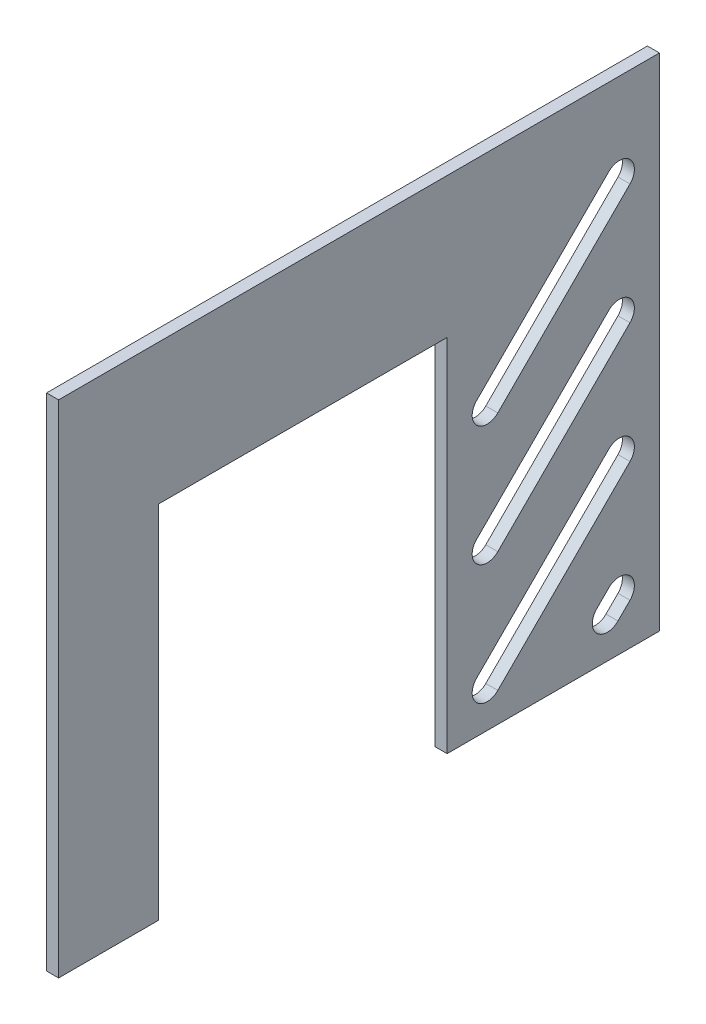
SolidWorks part; units mm, degrees
ref_plane "Front Plane" through (0, 0, 0) normal (0, 0, 1) x (1, 0, 0)
ref_plane "Top Plane" through (0, 0, 0) normal (0, 1, 0) x (1, 0, 0)
ref_plane "Right Plane" through (0, 0, 0) normal (1, 0, 0) x (0, 0, -1)
sketch "Sketch1" plane through (0, 0, 0) normal (1, 0, 0) x (0, 0, -1)
  line L0 (0, 0) -> (50, 0)
  line L2 (0, 0) -> (0, 250)
  line L3 (0, 250) -> (300, 250)
  line L4 (300, 0) -> (300, 250)
  line L5 (50, 0) -> (50, 180)
  line L6 (50, 180) -> (194, 180)
  line L7 (194, 180) -> (194, 0)
  line L8 (300, 0) -> (194, 0)
  line L9 (50, 0) -> (0, 0)
  line L10 (280, 20) -> (214, 86) construction
  line L11 (300, 0) -> (280, 0)
  line L12 (300, 0) -> (300, 20)
  line L13 (300, 20) -> (280, 20) construction
  line L14 (280, 0) -> (280, 20) construction
  line L15 (280, 20) -> (214, 20) construction
  line L16 (280, 20) -> (280, 86) construction
  line L17 (280, 86) -> (214, 86) construction
  line L18 (214, 20) -> (214, 86) construction
  line L19 (214, 86) -> (194, 86) construction
  line L20 (214, 86) -> (214, 106) construction
  line L21 (214, 106) -> (194, 106) construction
  line L22 (194, 86) -> (194, 106)
  line L23 (274.6967, 14.6967) -> (208.6967, 80.6967)
  line L24 (285.3033, 25.3033) -> (219.3033, 91.3033)
  arc A0 (274.6967, 14.6967) -> (285.3033, 25.3033) centre (280, 20) ccw
  arc A1 (219.3033, 91.3033) -> (208.6967, 80.6967) centre (214, 86) ccw
  point P18 (247, 53)
  dimension "D1" = 250
  dimension "D2" = 300
  dimension "D3" = 180
  dimension "D4" = 144
  dimension "D5" = 250
  dimension "D6" = 20
  dimension "D7" = 20
  dimension "D8" = 66
  dimension "D9" = 66
  dimension "D10" = 20
  dimension "D11" = 15
extrude "Boss-Extrude1" add sketch "Sketch1" along normal blind 6 contours L8 L4 L3 L2 L0 L5 L6 L7
sketch "Sketch2" plane through (0, 0, 0) normal (-1, 0, 0) x (0, 0, 1)
  line L0 (-194, 180) -> (-194, 0) construction
  line L1 (-300, 0) -> (-194, 0)
  line L2 (-300, 0) -> (-300, 107.9511)
  line L3 (-300, 107.9511) -> (-194, 107.9511)
  line L4 (-194, 0) -> (-194, 107.9511)
extrude "Boss-Extrude3" add sketch "Sketch2" against normal up to surface (6 mm away) up to face at (6, 53, -247)
sketch "Sketch3" plane through (0, 0, 0) normal (-1, 0, 0) x (0, 0, 1)
  line L0 (-194, 0) -> (-194, 288) construction
  line L1 (-300, 180) -> (-300, 0) construction
  line L2 (-194, 0) -> (-300, 0) construction
  line L3 (-214, 20) -> (-280, 86) construction
  line L4 (-194, 0) -> (-214, 0) construction
  line L5 (-194, 0) -> (-194, 20) construction
  line L6 (-194, 20) -> (-214, 20) construction
  line L7 (-214, 0) -> (-214, 20) construction
  line L8 (-214, 20) -> (-280, 20) construction
  line L9 (-214, 20) -> (-214, 86) construction
  line L10 (-214, 86) -> (-280, 86) construction
  line L11 (-280, 20) -> (-280, 86) construction
  line L12 (-280, 86) -> (-300, 86) construction
  line L13 (-280, 86) -> (-280, 106) construction
  line L14 (-280, 106) -> (-300, 106) construction
  line L15 (-300, 86) -> (-300, 106) construction
  line L16 (-219.3033, 14.6967) -> (-285.3033, 80.6967)
  line L17 (-208.6967, 25.3033) -> (-274.6967, 91.3033)
  line L18 (-280, 86) -> (-280, 26) construction
  line L19 (-214, 20) -> (-274, 20) construction
  line L20 (-274, 20) -> (-280, 26) construction
  line L21 (-279.3033, 14.6967) -> (-285.3033, 20.6967)
  line L22 (-268.6967, 25.3033) -> (-274.6967, 31.3033)
  line L23 (-194, 108) -> (-194, 288) construction
  line L24 (-300, 288) -> (-194, 288) construction
  line L25 (-280, 268) -> (-214, 268) construction
  line L26 (-214, 268) -> (-214, 202) construction
  line L27 (-214, 202) -> (-214, 262) construction
  line L28 (-280, 268) -> (-220, 268) construction
  line L29 (-220, 268) -> (-214, 262) construction
  line L30 (-214.6967, 273.3033) -> (-208.6967, 267.3033)
  line L31 (-225.3033, 262.6967) -> (-219.3033, 256.6967)
  arc A0 (-219.3033, 14.6967) -> (-208.6967, 25.3033) centre (-214, 20) ccw
  arc A1 (-274.6967, 91.3033) -> (-285.3033, 80.6967) centre (-280, 86) ccw
  arc A2 (-279.3033, 14.6967) -> (-268.6967, 25.3033) centre (-274, 20) ccw
  arc A3 (-274.6967, 31.3033) -> (-285.3033, 20.6967) centre (-280, 26) ccw
  arc A4 (-214.6967, 273.3033) -> (-225.3033, 262.6967) centre (-220, 268) ccw
  arc A5 (-219.3033, 256.6967) -> (-208.6967, 267.3033) centre (-214, 262) ccw
  point P13 (-247, 53)
  point P22 (-277, 23)
  point P37 (-217, 265)
  dimension "D10" = 7.5
  dimension "D15" = 7.5
  dimension "D1" = 288
  dimension "D2" = 20
  dimension "D3" = 20
  dimension "D4" = 66
  dimension "D5" = 66
  dimension "D6" = 20
  dimension "D7" = 15
  dimension "D8" = 60
  dimension "D9" = 60
  dimension "D11" = 66
  dimension "D12" = 66
  dimension "D13" = 60
  dimension "D14" = 60
extrude "Cut-Extrude1" cut sketch "Sketch3" against normal blind 10
pattern_linear "LPattern1" count 3 spacing 60 along (0, 1, 0) of "Cut-Extrude1"
